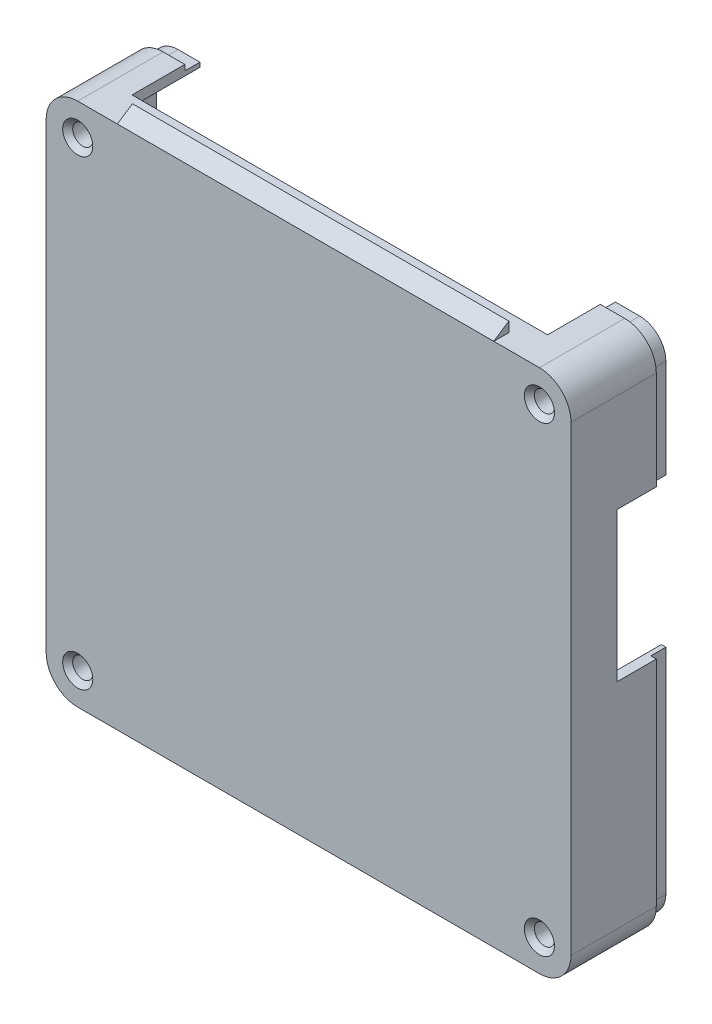
SolidWorks part; units mm, degrees
ref_plane "Front Plane" through (0, 0, 0) normal (0, 0, 1) x (1, 0, 0)
ref_plane "Top Plane" through (0, 0, 0) normal (0, 1, 0) x (1, 0, 0)
ref_plane "Right Plane" through (0, 0, 0) normal (1, 0, 0) x (0, 0, -1)
sketch "Sketch1" plane through (0, 0, 89.3526) normal (0, 0, 1) x (-1, 0, 0)
  circle A0 centre (-74.0994, 104.9557) radius 3.25
  circle A1 centre (17.9008, 104.9557) radius 3.25
  circle A2 centre (17.9008, 12.9555) radius 3.25
  circle A3 centre (-74.0994, 12.9555) radius 3.25
  dimension "D1" = 6.5
  dimension "D2" = 6.5
  dimension "D3" = 6.5
  dimension "D4" = 6.5
extrude "Boss-Extrude1" add sketch "Sketch1" along normal blind 3
sketch "Sketch2" plane through (0, 0, 92.3526) normal (0, 0, 1) x (-1, 0, 0)
  line L2 (17.9008, 109.243) -> (-74.0994, 109.243)
  line L3 (17.9008, 109.243) -> (-74.0994, 109.243)
  line L18 (22.1881, 12.9555) -> (22.1881, 104.9557)
  line L19 (-74.0994, 8.6682) -> (17.9008, 8.6682)
  line L20 (-78.3867, 104.9557) -> (-78.3867, 12.9555)
  line L21 (22.1881, 12.9555) -> (22.1881, 104.9557)
  line L22 (-74.0994, 8.6682) -> (17.9008, 8.6682)
  line L23 (-78.3867, 104.9557) -> (-78.3867, 12.9555)
  arc A20 (22.1881, 104.9557) -> (17.9008, 109.243) centre (17.9008, 104.9557) ccw
  arc A21 (17.9008, 8.6682) -> (22.1881, 12.9555) centre (17.9008, 12.9555) ccw
  arc A22 (-78.3867, 12.9555) -> (-74.0994, 8.6682) centre (-74.0994, 12.9555) ccw
  arc A23 (-74.0994, 109.243) -> (-78.3867, 104.9557) centre (-74.0994, 104.9557) ccw
  arc A24 (22.1881, 104.9557) -> (17.9008, 109.243) centre (17.9008, 104.9557) ccw
  arc A25 (17.9008, 8.6682) -> (22.1881, 12.9555) centre (17.9008, 12.9555) ccw
  arc A26 (-78.3867, 12.9555) -> (-74.0994, 8.6682) centre (-74.0994, 12.9555) ccw
  arc A27 (-74.0994, 109.243) -> (-78.3867, 104.9557) centre (-74.0994, 104.9557) ccw
  dimension "D1" = 0.3
  dimension "D2" = 0.3
extrude "Boss-Extrude2" add sketch "Sketch2" along normal blind 2
sketch "Sketch3" plane through (0, 0, 94.3526) normal (0, 0, 1) x (-1, 0, 0)
  line L10 (17.9008, 111.243) -> (-74.0994, 111.243)
  line L11 (-80.3867, 104.9557) -> (-80.3867, 12.9555)
  line L12 (17.9008, 111.243) -> (-74.0994, 111.243)
  line L13 (-80.3867, 104.9557) -> (-80.3867, 12.9555)
  line L18 (17.9008, 109.243) -> (-74.0994, 109.243) construction
  line L19 (17.9008, 109.243) -> (-74.0994, 109.243)
  line L20 (-74.0994, 6.6682) -> (17.9008, 6.6682)
  line L21 (24.1881, 12.9555) -> (24.1881, 104.9557)
  line L22 (-74.0994, 6.6682) -> (17.9008, 6.6682)
  line L23 (24.1881, 12.9555) -> (24.1881, 104.9557)
  line L24 (22.1881, 12.9555) -> (22.1881, 104.9557) construction
  line L25 (22.1881, 12.9555) -> (22.1881, 104.9557)
  line L26 (-78.3867, 104.9557) -> (-78.3867, 12.9555) construction
  line L27 (-74.0994, 8.6682) -> (17.9008, 8.6682) construction
  line L28 (-78.3867, 104.9557) -> (-78.3867, 12.9555)
  line L29 (-74.0994, 8.6682) -> (17.9008, 8.6682)
  arc A9 (24.1881, 104.9557) -> (17.9008, 111.243) centre (17.9008, 104.9557) ccw
  arc A10 (-74.0994, 111.243) -> (-80.3867, 104.9557) centre (-74.0994, 104.9557) ccw
  arc A11 (24.1881, 104.9557) -> (17.9008, 111.243) centre (17.9008, 104.9557) ccw
  arc A12 (-74.0994, 111.243) -> (-80.3867, 104.9557) centre (-74.0994, 104.9557) ccw
  arc A15 (22.1881, 104.9557) -> (17.9008, 109.243) centre (17.9008, 104.9557) ccw construction
  arc A16 (22.1881, 104.9557) -> (17.9008, 109.243) centre (17.9008, 104.9557) ccw
  arc A17 (-80.3867, 12.9555) -> (-74.0994, 6.6682) centre (-74.0994, 12.9555) ccw
  arc A18 (17.9008, 6.6682) -> (24.1881, 12.9555) centre (17.9008, 12.9555) ccw
  arc A19 (-80.3867, 12.9555) -> (-74.0994, 6.6682) centre (-74.0994, 12.9555) ccw
  arc A20 (17.9008, 6.6682) -> (24.1881, 12.9555) centre (17.9008, 12.9555) ccw
  arc A21 (17.9008, 8.6682) -> (22.1881, 12.9555) centre (17.9008, 12.9555) ccw construction
  arc A22 (17.9008, 8.6682) -> (22.1881, 12.9555) centre (17.9008, 12.9555) ccw
  arc A23 (-74.0994, 109.243) -> (-78.3867, 104.9557) centre (-74.0994, 104.9557) ccw construction
  arc A24 (-78.3867, 12.9555) -> (-74.0994, 8.6682) centre (-74.0994, 12.9555) ccw construction
  arc A25 (-74.0994, 109.243) -> (-78.3867, 104.9557) centre (-74.0994, 104.9557) ccw
  arc A26 (-78.3867, 12.9555) -> (-74.0994, 8.6682) centre (-74.0994, 12.9555) ccw
  dimension "D1" = 2
  dimension "D2" = 2
extrude "Boss-Extrude3" add sketch "Sketch3" against normal blind 20
sketch "Sketch4" plane through (0, 0, 89.3526) normal (0, 0, -1) x (1, 0, 0)
  circle A0 centre (-17.9008, 104.9557) radius 2
  circle A1 centre (74.0994, 104.9557) radius 2
  circle A2 centre (74.0994, 12.9555) radius 2
  circle A3 centre (-17.9008, 12.9555) radius 2
  dimension "D1" = 4
  dimension "D2" = 4
  dimension "D3" = 4
  dimension "D4" = 4
extrude "Cut-Extrude1" cut sketch "Sketch4" against normal up to surface (5 mm away) up to face at (28.0993, -58.9556, 94.3526)
ref_plane "Plane1" through (0.7808, -9.1475, 86.5972) normal (1, 0, 0) x (0, 0, -1)
sketch "Sketch6" plane through (0, -6.6682, 0) normal (0, 1, 0) x (1, 0, 0)
  line L0 (69.1377, -87.5681) -> (69.1377, -74.1343) construction
  line L1 (69.2377, -87.8665) -> (-13.5528, -87.8665)
  line L2 (69.2377, -87.8665) -> (69.2377, -73.8344)
  line L3 (69.2377, -73.8344) -> (-13.5528, -73.8344)
  line L4 (-13.5528, -87.8665) -> (-13.5528, -73.8344)
  line L5 (74.0994, -87.7665) -> (-17.9008, -87.7665) construction
  line L7 (68.9378, -73.9344) -> (53.6949, -73.9344) construction
  line L8 (-13.4528, -79.9665) -> (-13.4528, -87.7665) construction
  dimension "D1" = 0.1
  dimension "D2" = 0.1
  dimension "D3" = 0.1
  dimension "D4" = 0.1
extrude "Cut-Extrude2" cut sketch "Sketch6" against normal up to next
sketch "Sketch7" plane through (80.3867, 0, 0) normal (1, 0, 0) x (0, 0, -1)
  line L1 (-68.1664, -32.5945) -> (-85.1664, -32.5945)
  line L2 (-68.1664, -32.5945) -> (-68.1664, -62.2999)
  line L3 (-68.1664, -62.2999) -> (-85.1664, -62.2999)
  line L4 (-85.1664, -32.5945) -> (-85.1664, -62.2999)
  dimension "D1" = 17
extrude "Cut-Extrude3" cut sketch "Sketch7" against normal up to next
chamfer "Chamfer1" distance 1 angle 45 4 edges at (76.0994, -104.9557, 94.3526) (-15.9008, -104.9557, 94.3526) (76.0994, -12.9555, 94.3526) (-15.9008, -12.9555, 94.3526)
sketch "Sketch10" plane through (0, 0, 74.3526) normal (0, 0, -1) x (-1, 0, 0)
  line L48 (-80.3867, -12.9555) -> (-80.3867, -32.5945)
  line L49 (-80.3867, -32.5945) -> (-80.3867, -62.2999)
  line L50 (-80.3867, -62.2999) -> (-80.3867, -104.9557)
  line L51 (-74.0994, -111.243) -> (17.9008, -111.243)
  line L52 (24.1881, -104.9557) -> (24.1881, -12.9555)
  line L53 (17.9008, -6.6682) -> (13.5528, -6.6682)
  line L54 (13.5528, -6.6682) -> (-69.2377, -6.6682)
  line L55 (-69.2377, -6.6682) -> (-74.0994, -6.6682)
  line L56 (-79.2867, -32.5945) -> (-79.2867, -62.2999)
  line L57 (-79.2867, -12.9555) -> (-79.2867, -32.5945)
  line L58 (-69.2377, -7.7682) -> (-74.0994, -7.7682)
  line L59 (13.5528, -7.7682) -> (-69.2377, -7.7682)
  line L60 (17.9008, -7.7682) -> (13.5528, -7.7682)
  line L61 (23.0881, -104.9557) -> (23.0881, -12.9555)
  line L62 (-74.0994, -110.143) -> (17.9008, -110.143)
  line L63 (-79.2867, -62.2999) -> (-79.2867, -104.9557)
  line L64 (-79.2867, -32.5945) -> (-79.2867, -62.2999)
  line L65 (-79.2867, -12.9555) -> (-79.2867, -32.5945)
  line L66 (-69.2377, -7.7682) -> (-74.0994, -7.7682)
  line L67 (13.5528, -7.7682) -> (-69.2377, -7.7682)
  line L68 (17.9008, -7.7682) -> (13.5528, -7.7682)
  line L69 (23.0881, -104.9557) -> (23.0881, -12.9555)
  line L70 (-74.0994, -110.143) -> (17.9008, -110.143)
  line L71 (-79.2867, -62.2999) -> (-79.2867, -104.9557)
  arc A30 (-80.3867, -104.9557) -> (-74.0994, -111.243) centre (-74.0994, -104.9557) ccw
  arc A31 (17.9008, -111.243) -> (24.1881, -104.9557) centre (17.9008, -104.9557) ccw
  arc A32 (24.1881, -12.9555) -> (17.9008, -6.6682) centre (17.9008, -12.9555) ccw
  arc A33 (-74.0994, -6.6682) -> (-80.3867, -12.9555) centre (-74.0994, -12.9555) ccw
  arc A34 (-74.0994, -7.7682) -> (-79.2867, -12.9555) centre (-74.0994, -12.9555) ccw
  arc A35 (23.0881, -12.9555) -> (17.9008, -7.7682) centre (17.9008, -12.9555) ccw
  arc A36 (17.9008, -110.143) -> (23.0881, -104.9557) centre (17.9008, -104.9557) ccw
  arc A37 (-79.2867, -104.9557) -> (-74.0994, -110.143) centre (-74.0994, -104.9557) ccw
  arc A38 (-74.0994, -7.7682) -> (-79.2867, -12.9555) centre (-74.0994, -12.9555) ccw
  arc A39 (23.0881, -12.9555) -> (17.9008, -7.7682) centre (17.9008, -12.9555) ccw
  arc A40 (17.9008, -110.143) -> (23.0881, -104.9557) centre (17.9008, -104.9557) ccw
  arc A41 (-79.2867, -104.9557) -> (-74.0994, -110.143) centre (-74.0994, -104.9557) ccw
  dimension "D1" = 1.1
  dimension "D2" = 1.1
extrude "Cut-Extrude4" cut sketch "Sketch10" against normal blind 3
sketch "Sketch11" plane through (0, 0, 0) normal (1, 0, 0) x (0, 0, -1)
  line L0 (-94.3526, -6.6682) -> (-91.3526, -4.6682)
  line L1 (-91.3526, -4.6682) -> (-91.3526, -6.6682)
  line L2 (-77.3526, -6.6682) -> (-94.3526, -6.6682) construction
  line L3 (-91.3526, -6.6682) -> (-94.3526, -6.6682)
  line L4 (-94.3526, -111.243) -> (-91.3526, -111.243)
  line L5 (-77.3526, -111.243) -> (-94.3526, -111.243) construction
  line L6 (-91.3526, -111.243) -> (-91.3526, -113.243)
  line L7 (-91.3526, -113.243) -> (-94.3526, -111.243)
  dimension "D1" = 2
  dimension "D2" = 3
  dimension "D3" = 2
  dimension "D4" = 3
extrude "Boss-Extrude4" add sketch "Sketch11" along normal blind 65 and the other way blind 10
